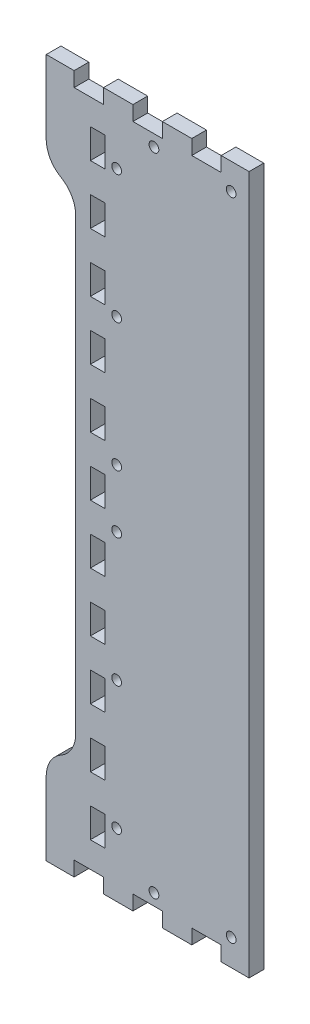
SolidWorks part; units mm, degrees
ref_plane "Front Plane" through (0, 0, 0) normal (0, 0, 1) x (1, 0, 0)
ref_plane "Top Plane" through (0, 0, 0) normal (0, 1, 0) x (1, 0, 0)
ref_plane "Right Plane" through (0, 0, 0) normal (1, 0, 0) x (0, 0, -1)
sketch "Model" plane through (0, 0, 0) normal (0, 0, 1) x (1, 0, 0)
  line L660 (953.262, 22.8575) -> (964.099, 22.8575)
  line L661 (964.099, 22.8575) -> (964.099, 28.5722)
  line L662 (964.099, 28.5722) -> (975.526, 28.5722)
  line L663 (975.526, 28.5722) -> (975.526, 22.8575)
  line L664 (975.526, 22.8575) -> (986.956, 22.8575)
  line L665 (986.956, 22.8575) -> (986.956, 28.5722)
  line L666 (986.956, 28.5722) -> (998.386, 28.5722)
  line L667 (998.386, 28.5722) -> (998.386, 22.8575)
  line L668 (998.386, 22.8575) -> (1009.82, 22.8575)
  line L669 (1009.82, 22.8575) -> (1009.82, 28.5722)
  line L670 (1009.82, 28.5722) -> (1021.25, 28.5722)
  line L671 (1021.25, 28.5722) -> (1021.25, 22.8575)
  line L672 (1021.25, 22.8575) -> (1032.08, 22.8575)
  line L673 (1032.08, 22.8575) -> (1032.08, 28.5722)
  line L674 (1032.08, 28.5722) -> (1032.08, 288.572)
  line L675 (1032.08, 288.572) -> (1032.08, 294.287)
  line L676 (1032.08, 294.287) -> (1021.25, 294.287)
  line L677 (1021.25, 294.287) -> (1021.25, 288.572)
  line L678 (1021.25, 288.572) -> (1009.82, 288.572)
  line L679 (1009.82, 288.572) -> (1009.82, 294.287)
  line L680 (1009.82, 294.287) -> (998.386, 294.287)
  line L681 (998.386, 294.287) -> (998.386, 288.572)
  line L682 (998.386, 288.572) -> (986.956, 288.572)
  line L683 (986.956, 288.572) -> (986.956, 294.287)
  line L684 (986.956, 294.287) -> (975.526, 294.287)
  line L685 (975.526, 294.287) -> (975.526, 288.572)
  line L686 (975.526, 288.572) -> (964.099, 288.572)
  line L687 (964.099, 288.572) -> (964.099, 294.287)
  line L688 (964.099, 294.287) -> (953.262, 294.287)
  line L689 (953.262, 294.287) -> (953.262, 288.572)
  line L690 (953.262, 288.572) -> (953.262, 265.712)
  line L691 (953.262, 265.712) -> (953.262, 265.339)
  line L692 (953.262, 265.339) -> (953.361, 264.218)
  line L693 (953.361, 264.218) -> (953.654, 262.755)
  line L694 (953.654, 262.755) -> (954.133, 261.342)
  line L695 (954.133, 261.342) -> (954.606, 260.321)
  line L696 (954.606, 260.321) -> (954.793, 259.997)
  line L697 (954.793, 259.997) -> (954.888, 259.836)
  line L698 (954.888, 259.836) -> (955.192, 259.36)
  line L699 (955.192, 259.36) -> (955.626, 258.753)
  line L700 (955.626, 258.753) -> (956.098, 258.175)
  line L701 (956.098, 258.175) -> (956.61, 257.631)
  line L702 (956.61, 257.631) -> (957.153, 257.121)
  line L703 (957.153, 257.121) -> (957.732, 256.647)
  line L704 (957.732, 256.647) -> (958.338, 256.211)
  line L705 (958.338, 256.211) -> (958.815, 255.907)
  line L706 (958.815, 255.907) -> (958.977, 255.814)
  line L707 (958.977, 255.814) -> (959.139, 255.721)
  line L708 (959.139, 255.721) -> (959.612, 255.418)
  line L709 (959.612, 255.418) -> (960.222, 254.981)
  line L710 (960.222, 254.981) -> (960.801, 254.507)
  line L711 (960.801, 254.507) -> (961.344, 253.997)
  line L712 (961.344, 253.997) -> (961.856, 253.453)
  line L713 (961.856, 253.453) -> (962.328, 252.876)
  line L714 (962.328, 252.876) -> (962.766, 252.268)
  line L715 (962.766, 252.268) -> (963.069, 251.792)
  line L716 (963.069, 251.792) -> (963.161, 251.63)
  line L717 (963.161, 251.63) -> (963.348, 251.307)
  line L718 (963.348, 251.307) -> (963.824, 250.286)
  line L719 (963.824, 250.286) -> (964.304, 248.874)
  line L720 (964.304, 248.874) -> (964.593, 247.41)
  line L721 (964.593, 247.41) -> (964.692, 246.29)
  line L722 (964.692, 246.29) -> (964.692, 245.915)
  line L723 (964.692, 245.915) -> (964.692, 71.2294)
  line L724 (964.692, 71.2294) -> (964.692, 70.8561)
  line L725 (964.692, 70.8561) -> (964.593, 69.7357)
  line L726 (964.593, 69.7357) -> (964.304, 68.272)
  line L727 (964.304, 68.272) -> (963.824, 66.8595)
  line L728 (963.824, 66.8595) -> (963.348, 65.8386)
  line L729 (963.348, 65.8386) -> (963.161, 65.5147)
  line L730 (963.161, 65.5147) -> (963.069, 65.3535)
  line L731 (963.069, 65.3535) -> (962.766, 64.878)
  line L732 (962.766, 64.878) -> (962.328, 64.2705)
  line L733 (962.328, 64.2705) -> (961.856, 63.693)
  line L734 (961.856, 63.693) -> (961.344, 63.1486)
  line L735 (961.344, 63.1486) -> (960.801, 62.6389)
  line L736 (960.801, 62.6389) -> (960.222, 62.1647)
  line L737 (960.222, 62.1647) -> (959.612, 61.728)
  line L738 (959.612, 61.728) -> (959.139, 61.4246)
  line L739 (959.139, 61.4246) -> (958.977, 61.3311)
  line L740 (958.977, 61.3311) -> (958.815, 61.2373)
  line L741 (958.815, 61.2373) -> (958.338, 60.9353)
  line L742 (958.338, 60.9353) -> (957.732, 60.4986)
  line L743 (957.732, 60.4986) -> (957.153, 60.0244)
  line L744 (957.153, 60.0244) -> (956.61, 59.5147)
  line L745 (956.61, 59.5147) -> (956.098, 58.9703)
  line L746 (956.098, 58.9703) -> (955.626, 58.3928)
  line L747 (955.626, 58.3928) -> (955.192, 57.7854)
  line L748 (955.192, 57.7854) -> (954.888, 57.3098)
  line L749 (954.888, 57.3098) -> (954.793, 57.1472)
  line L750 (954.793, 57.1472) -> (954.606, 56.8247)
  line L751 (954.606, 56.8247) -> (954.133, 55.8038)
  line L752 (954.133, 55.8038) -> (953.654, 54.3913)
  line L753 (953.654, 54.3913) -> (953.361, 52.9276)
  line L754 (953.361, 52.9276) -> (953.262, 51.8072)
  line L755 (953.262, 51.8072) -> (953.262, 51.4325)
  line L756 (953.262, 51.4325) -> (953.262, 28.5722)
  line L757 (953.262, 28.5722) -> (953.262, 22.8575)
  line L758 (970.407, 272.872) -> (970.407, 278.587)
  line L759 (970.407, 278.587) -> (976.122, 278.587)
  line L760 (976.122, 278.587) -> (976.122, 267.158)
  line L761 (976.122, 267.158) -> (970.407, 267.158)
  line L762 (970.407, 267.158) -> (970.407, 272.872)
  line L763 (970.407, 250.012) -> (970.407, 255.728)
  line L764 (970.407, 255.728) -> (976.122, 255.728)
  line L765 (976.122, 255.728) -> (976.122, 244.297)
  line L766 (976.122, 244.297) -> (970.407, 244.297)
  line L767 (970.407, 244.297) -> (970.407, 250.012)
  line L768 (970.407, 227.153) -> (970.407, 232.868)
  line L769 (970.407, 232.868) -> (976.122, 232.868)
  line L770 (976.122, 232.868) -> (976.122, 221.437)
  line L771 (976.122, 221.437) -> (970.407, 221.437)
  line L772 (970.407, 221.437) -> (970.407, 227.153)
  line L773 (970.407, 204.293) -> (970.407, 210.008)
  line L774 (970.407, 210.008) -> (976.122, 210.008)
  line L775 (976.122, 210.008) -> (976.122, 198.578)
  line L776 (976.122, 198.578) -> (970.407, 198.578)
  line L777 (970.407, 198.578) -> (970.407, 204.293)
  line L778 (970.407, 181.433) -> (970.407, 187.147)
  line L779 (970.407, 187.147) -> (976.122, 187.147)
  line L780 (976.122, 187.147) -> (976.122, 175.718)
  line L781 (976.122, 175.718) -> (970.407, 175.718)
  line L782 (970.407, 175.718) -> (970.407, 181.433)
  line L783 (970.407, 158.572) -> (970.407, 164.287)
  line L784 (970.407, 164.287) -> (976.122, 164.287)
  line L785 (976.122, 164.287) -> (976.122, 152.858)
  line L786 (976.122, 152.858) -> (970.407, 152.858)
  line L787 (970.407, 152.858) -> (970.407, 158.572)
  line L788 (970.407, 135.712) -> (970.407, 141.428)
  line L789 (970.407, 141.428) -> (976.122, 141.428)
  line L790 (976.122, 141.428) -> (976.122, 129.997)
  line L791 (976.122, 129.997) -> (970.407, 129.997)
  line L792 (970.407, 129.997) -> (970.407, 135.712)
  line L793 (970.407, 112.853) -> (970.407, 118.568)
  line L794 (970.407, 118.568) -> (976.122, 118.568)
  line L795 (976.122, 118.568) -> (976.122, 107.137)
  line L796 (976.122, 107.137) -> (970.407, 107.137)
  line L797 (970.407, 107.137) -> (970.407, 112.853)
  line L798 (970.407, 89.9929) -> (970.407, 95.7076)
  line L799 (970.407, 95.7076) -> (976.122, 95.7076)
  line L800 (976.122, 95.7076) -> (976.122, 84.2779)
  line L801 (976.122, 84.2779) -> (970.407, 84.2779)
  line L802 (970.407, 84.2779) -> (970.407, 89.9929)
  line L803 (970.407, 67.1326) -> (970.407, 72.8472)
  line L804 (970.407, 72.8472) -> (976.122, 72.8472)
  line L805 (976.122, 72.8472) -> (976.122, 61.4179)
  line L806 (976.122, 61.4179) -> (970.407, 61.4179)
  line L807 (970.407, 61.4179) -> (970.407, 67.1326)
  line L808 (970.407, 44.2722) -> (970.407, 49.9868)
  line L809 (970.407, 49.9868) -> (976.122, 49.9868)
  line L810 (976.122, 49.9868) -> (976.122, 38.5576)
  line L811 (976.122, 38.5576) -> (970.407, 38.5576)
  line L812 (970.407, 38.5576) -> (970.407, 44.2722)
extrude "Boss-Extrude1" add sketch "Model" along normal blind 5.715
sketch "Sketch1" plane through (0, 0, 5.715) normal (0, 0, 1) x (1, 0, 0)
  point P0 (995.122, 33.0722)
  point P1 (1025.122, 33.0722)
  point P3 (1025.122, 284.072)
  point P5 (995.122, 284.072)
  point P7 (980.622, 269.572)
  point P9 (980.622, 219.7139)
  point P11 (980.622, 169.8557)
  point P13 (980.622, 47.5722)
  point P15 (980.622, 97.4303)
  point P17 (980.622, 147.2884)
hole_wizard "#6 Clearance Hole1" positions "Sketch2" profile "Sketch4" hole size "#6" standard "ANSI Inch" end condition through all
sketch "Sketch2" plane through (0, 0, 5.715) normal (0, 0, 1) x (1, 0, 0)
  point P0 (1025.122, 284.072)
  point P3 (995.122, 284.072)
  point P6 (980.622, 269.572)
  point P9 (980.622, 219.7139)
  point P12 (980.622, 169.8557)
  point P15 (980.622, 147.2884)
  point P18 (980.622, 97.4303)
  point P21 (980.622, 47.5722)
  point P24 (995.122, 33.0722)
  point P27 (1025.122, 33.0722)
sketch "Sketch4" plane through (1025.122, 284.072, 5.715) normal (1, 0, 0) x (0, -1, 0)
  line L0 (0, 0) -> (0, 5.715)
  line L1 (0, 5.715) -> (1.8986, 5.715)
  line L2 (1.8986, 5.715) -> (1.8986, 0)
  line L5 (1.8986, 0) -> (0, 0)
  line L11 (0, -6.35) -> (0, 107.95) construction
  dimension "Thru Hole Dia." = 3.7973
  dimension "Thru Hole Depth" = 5.715
